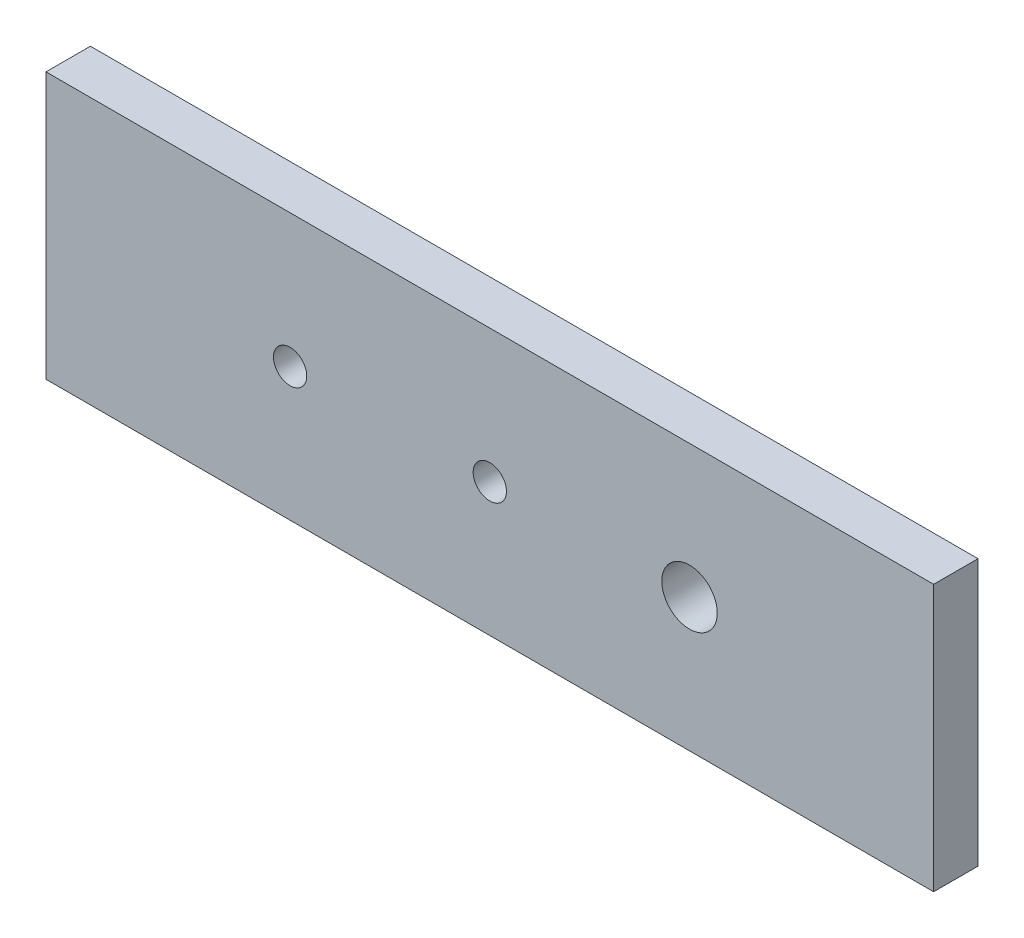
SolidWorks part; units mm, degrees
ref_plane "Front Plane" through (0, 0, 0) normal (0, 0, 1) x (1, 0, 0)
ref_plane "Top Plane" through (0, 0, 0) normal (0, 1, 0) x (1, 0, 0)
ref_plane "Right Plane" through (0, 0, 0) normal (1, 0, 0) x (0, 0, -1)
sketch "Sketch1" plane through (0, 0, 0) normal (0, 0, 1) x (1, 0, 0)
  line L1 (-254, -76.2) -> (254, -76.2)
  line L2 (-254, -76.2) -> (-254, 76.2)
  line L3 (-254, 76.2) -> (254, 76.2)
  line L4 (254, -76.2) -> (254, 76.2)
  line L5 (-254, -76.2) -> (254, 76.2) construction
  line L6 (-254, 76.2) -> (254, -76.2) construction
  circle A0 centre (-114.3, 0) radius 9.525
  circle A1 centre (0, 0) radius 9.525
  circle A2 centre (114.3, 0) radius 15.875
  point P0 (0, 0)
  dimension "D3" = 19.05
  dimension "D4" = 19.05
  dimension "D5" = 31.75
  dimension "D8" = 76.2
  dimension "D9" = 76.2
  dimension "D1" = 152.4
  dimension "D2" = 508
  dimension "D6" = 114.3
  dimension "D7" = 114.3
extrude "Boss-Extrude1" add sketch "Sketch1" along normal blind 25.4
